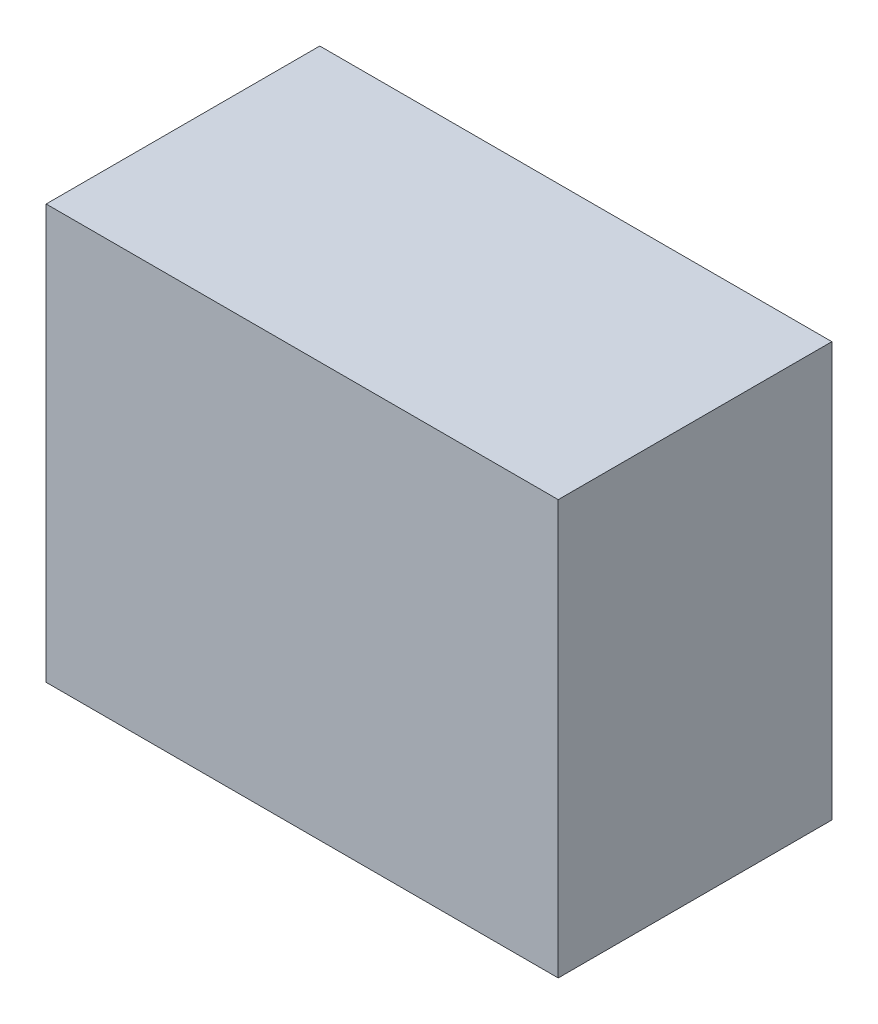
SolidWorks part; units mm, degrees
ref_plane "Front Plane" through (0, 0, 0) normal (0, 0, 1) x (1, 0, 0)
ref_plane "Top Plane" through (0, 0, 0) normal (0, 1, 0) x (1, 0, 0)
ref_plane "Right Plane" through (0, 0, 0) normal (1, 0, 0) x (0, 0, -1)
sketch "Sketch1" plane through (0, 0, 0) normal (0, 0, 1) x (1, 0, 0)
  line L1 (23.3, -18.85) -> (-23.3, -18.85)
  line L2 (23.3, -18.85) -> (23.3, 18.85)
  line L3 (23.3, 18.85) -> (-23.3, 18.85)
  line L4 (-23.3, -18.85) -> (-23.3, 18.85)
  line L5 (23.3, -18.85) -> (-23.3, 18.85) construction
  line L6 (23.3, 18.85) -> (-23.3, -18.85) construction
  point P0 (0, 0)
  dimension "D1" = 46.6
  dimension "D2" = 37.7
extrude "Boss-Extrude1" add sketch "Sketch1" along normal blind 24.9
